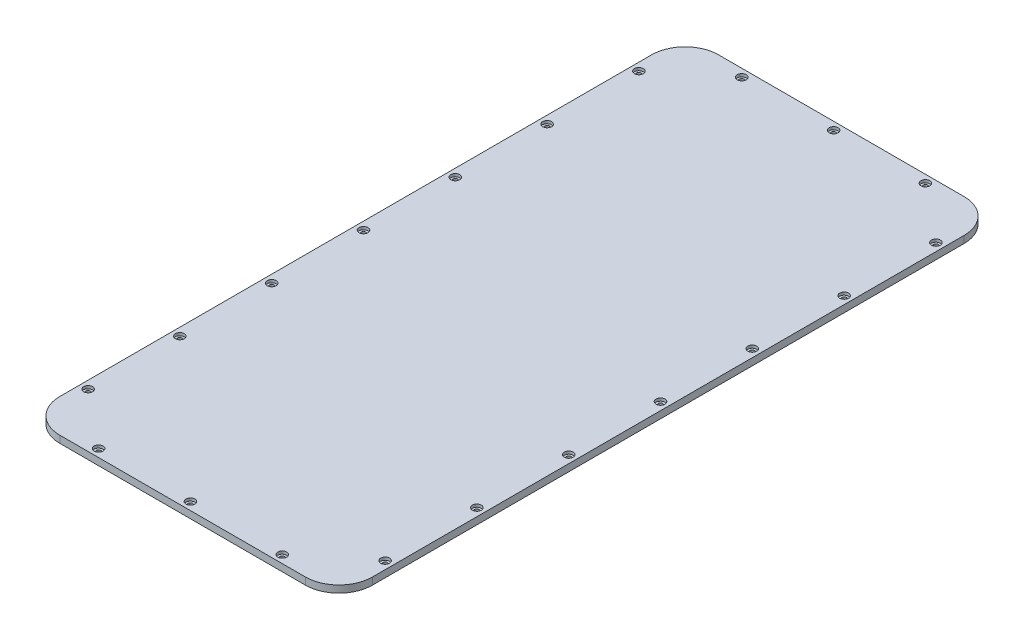
SolidWorks part; units mm, degrees
material "Acrylic (Medium-high impact)"
ref_plane "Front Plane" through (0, 0, 0) normal (0, 0, 1) x (1, 0, 0)
ref_plane "Top Plane" through (0, 0, 0) normal (0, 1, 0) x (1, 0, 0)
ref_plane "Right Plane" through (0, 0, 0) normal (1, 0, 0) x (0, 0, -1)
sketch "Sketch1" plane through (0, 0, 0) normal (0, 1, 0) x (-1, 0, 0)
  line L8 (90.9274, 302.9312) -> (-129.0726, 302.9312)
  line L9 (-159.0726, 272.9312) -> (-159.0726, -257.0688)
  line L10 (-129.0726, -287.0688) -> (90.9274, -287.0688)
  line L11 (120.9274, -257.0688) -> (120.9274, 272.9312)
  arc A8 (-129.0726, 302.9312) -> (-159.0726, 272.9312) centre (-129.0726, 272.9312) ccw
  arc A9 (-159.0726, -257.0688) -> (-129.0726, -287.0688) centre (-129.0726, -257.0688) ccw
  arc A10 (90.9274, -287.0688) -> (120.9274, -257.0688) centre (90.9274, -257.0688) ccw
  arc A11 (120.9274, 272.9312) -> (90.9274, 302.9312) centre (90.9274, 272.9312) ccw
  circle A19 centre (-152.0726, 254.6082) radius 2.1
  circle A20 centre (-101.2983, 295.9312) radius 2.1
  circle A21 centre (-19.0726, 295.9312) radius 2.1
  circle A22 centre (63.1531, 295.9312) radius 2.1
  circle A23 centre (113.9274, 254.6082) radius 2.1
  circle A39 centre (-152.0726, 7.9312) radius 2.1
  circle A40 centre (-152.0726, -74.2945) radius 2.1
  circle A41 centre (-152.0726, -156.5202) radius 2.1
  circle A42 centre (-152.0726, -238.7458) radius 2.1
  circle A43 centre (-101.2983, -280.0688) radius 2.1
  circle A44 centre (-19.0726, -280.0688) radius 2.1
  circle A45 centre (63.1531, -280.0688) radius 2.1
  circle A46 centre (113.9274, -238.7458) radius 2.1
  circle A47 centre (113.9274, -156.5202) radius 2.1
  circle A48 centre (113.9274, -74.2945) radius 2.1
  circle A49 centre (113.9274, 7.9312) radius 2.1
  circle A50 centre (-152.0726, 90.1568) radius 2.1
  circle A51 centre (-152.0726, 172.3825) radius 2.1
  circle A52 centre (113.9274, 90.1568) radius 2.1
  circle A53 centre (113.9274, 172.3825) radius 2.1
  dimension "D2" = 4.2
extrude "Boss-Extrude1" add sketch "Sketch1" along normal blind 6.35
sketch "Sketch3" plane through (0, 6.35, 0) normal (0, 1, 0) x (1, 0, 0)
  circle A0 centre (152.0726, -254.6082) radius 4
  circle A1 centre (101.2983, -295.9312) radius 4
  circle A2 centre (19.0726, -295.9312) radius 4
  circle A3 centre (-63.1531, -295.9312) radius 4
  circle A4 centre (-113.9274, -254.6082) radius 4
  circle A5 centre (-113.9274, -172.3825) radius 4
  circle A6 centre (-113.9274, -90.1568) radius 4
  circle A7 centre (-113.9274, -7.9312) radius 4
  circle A8 centre (-113.9274, 74.2945) radius 4
  circle A9 centre (-113.9274, 156.5202) radius 4
  circle A10 centre (-113.9274, 238.7458) radius 4
  circle A11 centre (-63.1531, 280.0688) radius 4
  circle A12 centre (19.0726, 280.0688) radius 4
  circle A13 centre (101.2983, 280.0688) radius 4
  circle A14 centre (152.0726, 238.7458) radius 4
  circle A15 centre (152.0726, 156.5202) radius 4
  circle A16 centre (152.0726, 74.2945) radius 4
  circle A17 centre (152.0726, -7.9312) radius 4
  circle A18 centre (152.0726, -90.1568) radius 4
  circle A19 centre (152.0726, -172.3825) radius 4
  dimension "D1" = 8
extrude "Cut-Extrude1" cut sketch "Sketch3" against normal blind 2.5
